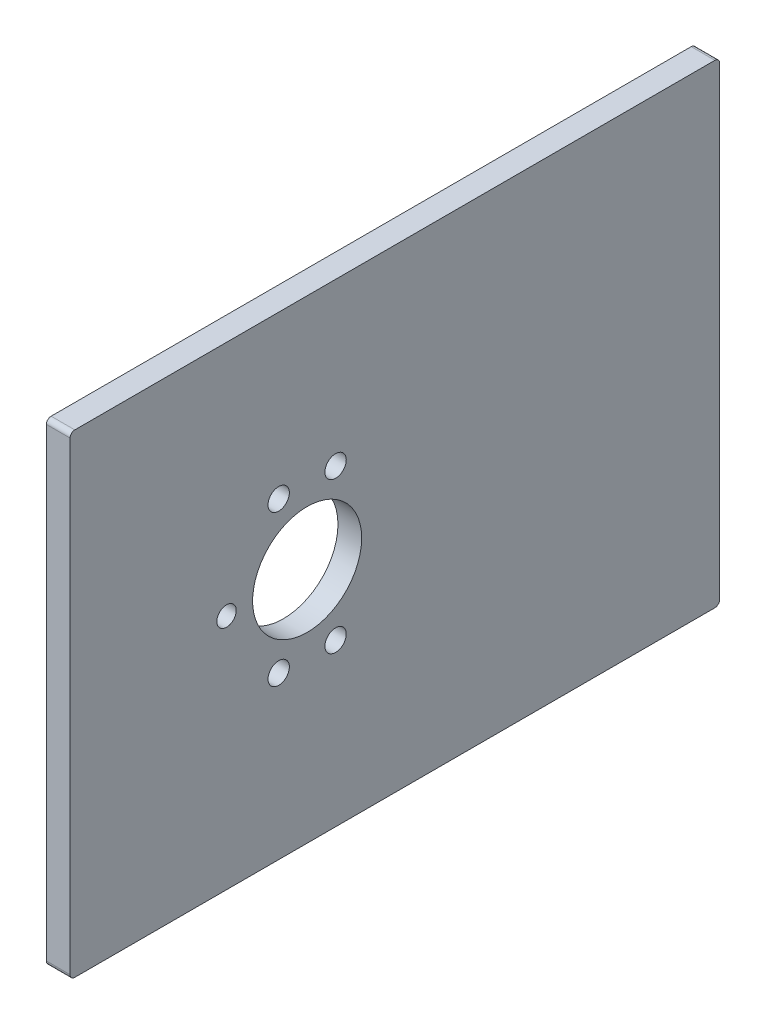
SolidWorks part; units mm, degrees
ref_plane "Ebene vorne" through (0, 0, 0) normal (0, 0, 1) x (1, 0, 0)
ref_plane "Ebene oben" through (0, 0, 0) normal (0, 1, 0) x (1, 0, 0)
ref_plane "Ebene rechts" through (0, 0, 0) normal (1, 0, 0) x (0, 0, -1)
sketch "Skizze1" plane through (0, 0, 0) normal (1, 0, 0) x (0, 0, -1)
  line L1 (-92, 59.9082) -> (-192, 59.9082)
  line L2 (-92, 59.9082) -> (-92, -40.0918) construction
  line L3 (-92, -40.0918) -> (-192, -40.0918)
  line L4 (-192, 59.9082) -> (-192, -40.0918)
  line L5 (-92, 59.9082) -> (-192, -40.0918) construction
  line L6 (-92, -40.0918) -> (-192, 59.9082) construction
  line L7 (-192, -40.0918) -> (-92, -40.0918) construction
  line L11 (-92, -40.0918) -> (-55, -40.0918)
  line L12 (-92, -40.0918) -> (-92, 59.9082) construction
  line L13 (-92, 59.9082) -> (-55, 59.9082)
  line L14 (-55, -40.0918) -> (-55, 59.9082)
  circle A0 centre (-142, 9.9082) radius 11.5
  circle A1 centre (-148, 25.8142) radius 2.25
  circle A2 centre (-136, 25.8142) radius 2.25
  circle A3 centre (-159, 9.9082) radius 2.05
  circle A4 centre (-148, -5.9978) radius 2.25
  circle A5 centre (-136, -5.9978) radius 2.25
  point P1 (-142, 9.9082)
  dimension "D3" = 23
  dimension "D4" = 4.5
  dimension "D6" = 4.1
  dimension "D1" = 100
  dimension "D2" = 100
  dimension "D5" = 87
extrude "Aufsatz-Linear austragen1" add sketch "Skizze1" along normal blind 5
fillet "Verrundung1" radius 1 4 edges at (2.5, 59.9082, 55) (2.5, -40.0918, 55) (2.5, 59.9082, 192) (2.5, -40.0918, 192)
